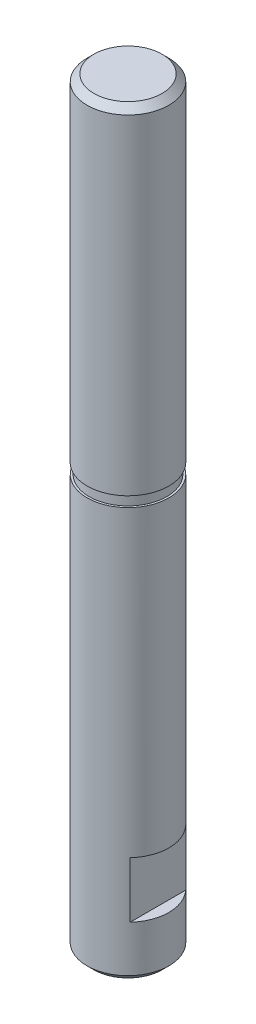
SolidWorks part; units mm, degrees
material "Plain Carbon Steel"
ref_plane "Front Plane" through (0, 0, 0) normal (0, 0, 1) x (1, 0, 0)
ref_plane "Top Plane" through (0, 0, 0) normal (0, 1, 0) x (1, 0, 0)
ref_plane "Right Plane" through (0, 0, 0) normal (1, 0, 0) x (0, 0, -1)
sketch "Sketch1" plane through (0, 0, 0) normal (0, 1, 0) x (1, 0, 0)
  circle A0 centre (0, 0) radius 3
  dimension "D1" = 6
extrude "Boss-Extrude1" add sketch "Sketch1" along normal blind 55.7
sketch "Sketch2" plane through (0, 0, 0) normal (0, 0, 1) x (1, 0, 0)
  line L0 (-3, 55.7) -> (-3, 0) construction
  line L1 (-3, 8) -> (-2.2, 8)
  line L2 (-3, 8) -> (-3, 3.9)
  line L3 (-3, 3.9) -> (-2.2, 3.9)
  line L4 (-2.2, 8) -> (-2.2, 3.9)
  line L9 (-3, 0) -> (3, 0) construction
  dimension "D1" = 3.9
  dimension "D2" = 0.8
  dimension "D3" = 4.1
extrude "Cut-Extrude1" cut sketch "Sketch2" against normal through all both and the other way through all
mirror "Mirror1" about plane through (0, 0, 0) normal (1, 0, 0) of "Cut-Extrude1"
ref_axis "Axis1" through (0, 55.7, 0) along (0, -1, 0)
sketch "Sketch3" plane through (0, 0, 0) normal (0, 0, 1) x (1, 0, 0)
  line L0 (3, 8) -> (3, 55.7) construction
  line L1 (3, 30.25) -> (2.85, 30.25)
  line L2 (3, 30.25) -> (3, 31)
  line L3 (3, 31) -> (2.85, 31)
  line L4 (2.85, 30.25) -> (2.85, 31)
  line L5 (-3, 0) -> (3, 0) construction
  dimension "D1" = 31
  dimension "D2" = 0.75
  dimension "D3" = 0.15
revolve "Cut-Revolve1" cut sketch "Sketch3" angle 360 about axis through (0, 55.7, 0) along (0, -1, 0)
chamfer "Chamfer1" distance 0.5 angle 45 2 edges at (0, 0, 3) (0, 55.7, 3)
